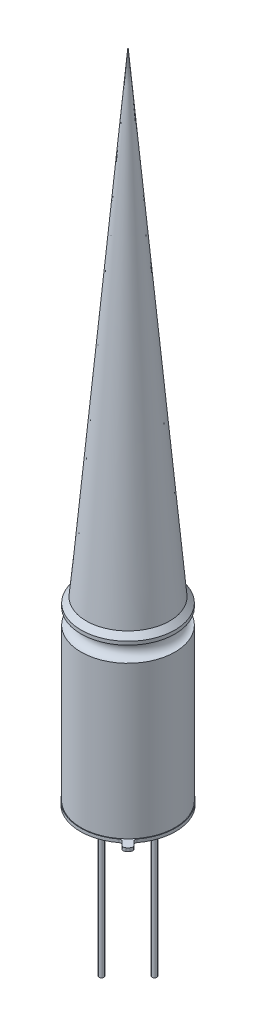
SolidWorks part; units mm, degrees
ref_plane "Front Plane" through (0, 0, 0) normal (0, 0, 1) x (1, 0, 0)
ref_plane "Top Plane" through (0, 0, 0) normal (0, 1, 0) x (1, 0, 0)
ref_plane "Right Plane" through (0, 0, 0) normal (1, 0, 0) x (0, 0, -1)
sketch "Sketch2" plane through (0, 0, 0) normal (0, 0, 1) x (1, 0, 0)
  line L0 (0, 11.5793) -> (0, -17.2) construction
  line L1 (4, 0) -> (4.5, -0.5)
  line L2 (0, 0) -> (4.5, 0)
  line L3 (0, 0) -> (0, -17.2)
  line L4 (0, -17.2) -> (4.56, -17.2)
  line L5 (4.5, 0) -> (4.5, -0.83)
  line L6 (4.5, -2.33) -> (4.5, -16.9)
  line L7 (0, -17.2) -> (0, -46.5882) construction
  line L8 (0, -17.2) -> (4.56, -17.2)
  line L10 (4.5, -16.9) -> (4.56, -16.9)
  line L11 (4.56, -17.2) -> (4.56, -16.9)
  arc A0 (4.5, -0.83) -> (4.5, -2.33) centre (4.5, -1.58) ccw
  dimension "D3" = 1.5
  dimension "D1" = 4.56
  dimension "D2" = 4.5
  dimension "D4" = 1.58
  dimension "D5" = 45
  dimension "D6" = 0.5
  dimension "D7" = 17.2
  dimension "D8" = 0.3
revolve "Revolve1" add sketch "Sketch2" angle 360 about L0
sketch "Sketch3" plane through (0, -17.2, 0) normal (0, -1, 0) x (1, 0, 0)
  line L0 (0, 4.9499) -> (0, -5.0471) construction
  line L1 (5.1504, 0) -> (-5.199, 0) construction
  circle A0 centre (0, 0) radius 2.54 construction
  circle A1 centre (-2.54, 0) radius 0.225
  circle A3 centre (0, 2.54) radius 0.225
  circle A4 centre (2.54, 0) radius 0.225
  circle A5 centre (0, -2.54) radius 0.225
  point P17 (0, 0)
  dimension "D1" = 5.08
  dimension "D2" = 0.45
  dimension "D3" = 4
extrude "Boss-Extrude1" add sketch "Sketch3" along normal blind 13
sketch "Sketch4" plane through (0, -17.2, 0) normal (0, -1, 0) x (1, 0, 0)
  line L0 (0, 0) -> (4.7612, 4.7612) construction
  line L1 (5.1504, 0) -> (-5.199, 0) construction
  line L3 (2.9291, 3.4948) -> (3.6362, 4.2019)
  line L4 (3.4948, 2.9291) -> (4.2019, 3.6362)
  line L5 (3.6362, 4.2019) -> (4.2019, 3.6362)
  circle A1 centre (0, 0) radius 4.56 construction
  arc A2 (3.4948, 2.9291) -> (2.9291, 3.4948) centre (0, 0) ccw
  dimension "D1" = 45
  dimension "D2" = 0.8
  dimension "D3" = 1
extrude "Boss-Extrude2" add sketch "Sketch4" against normal up to surface (0.3 mm away) up to face at (0, -16.9, 4.56)
fillet "Fillet1" radius 0.25 4 edges at (3.4948, -17.05, 2.9291) (4.2019, -17.05, 3.6362) (3.6362, -17.05, 4.2019) (2.9291, -17.05, 3.4948)
sketch "Sketch6" plane through (0, 0, 0) normal (0, 0, 1) x (1, 0, 0)
  line L0 (0, 0) -> (0, 45.7202)
  line L1 (0, 45.7202) -> (4, 0)
  line L2 (4, 0) -> (0, 0)
  dimension "D1" = 5
revolve "Revolve2" add sketch "Sketch6" angle 360 about L0
